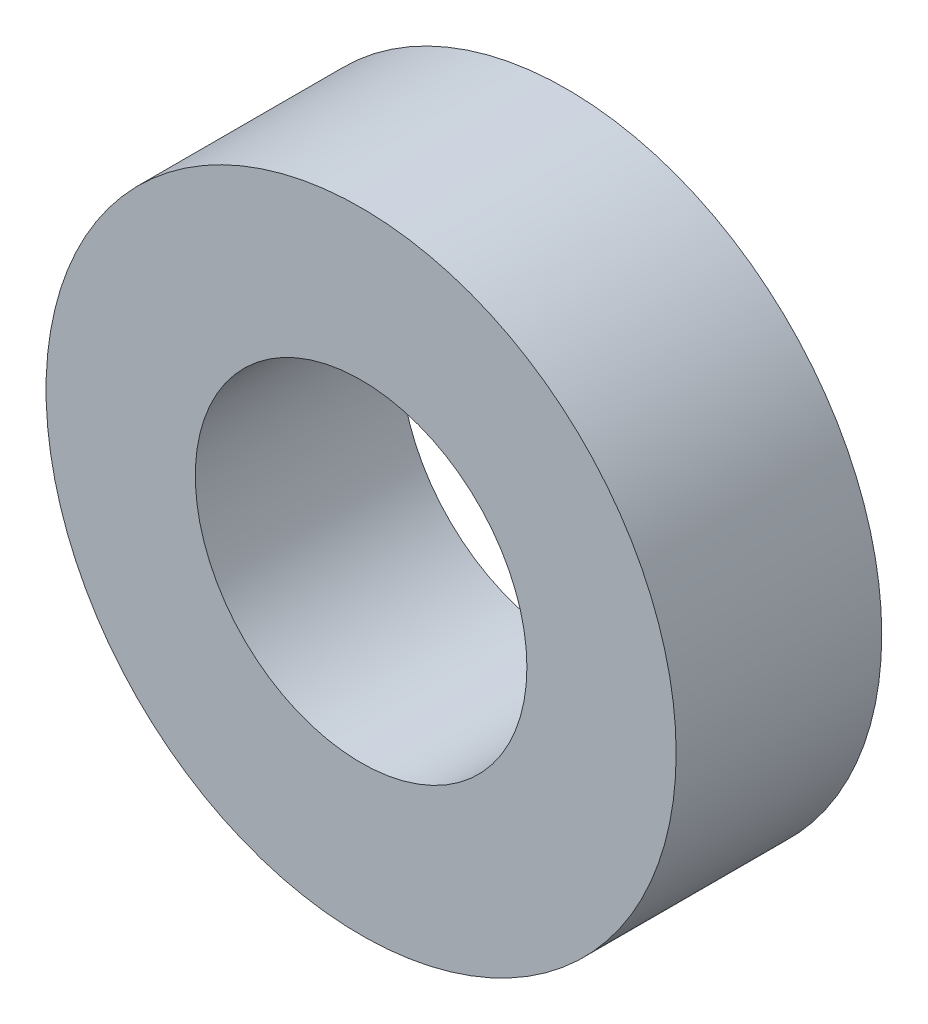
SolidWorks part; units mm, degrees
material "Nylon"
ref_plane "Front Plane" through (0, 0, 0) normal (0, 0, 1) x (1, 0, 0)
ref_plane "Top Plane" through (0, 0, 0) normal (0, 1, 0) x (1, 0, 0)
ref_plane "Right Plane" through (0, 0, 0) normal (1, 0, 0) x (0, 0, -1)
sketch "Sketch1" plane through (0, 0, 0) normal (0, 0, 1) x (1, 0, 0)
  circle A0 centre (0, 0) radius 4.75
  dimension "D1" = 9.5
extrude "Extrude1" add sketch "Sketch1" against normal blind 3.1
sketch "Sketch2" plane through (0, 0, 0) normal (0, 0, 1) x (1, 0, 0)
  circle A0 centre (0, 0) radius 2.5
  dimension "D1" = 5
extrude "Cut-Extrude1" cut sketch "Sketch2" against normal through all
